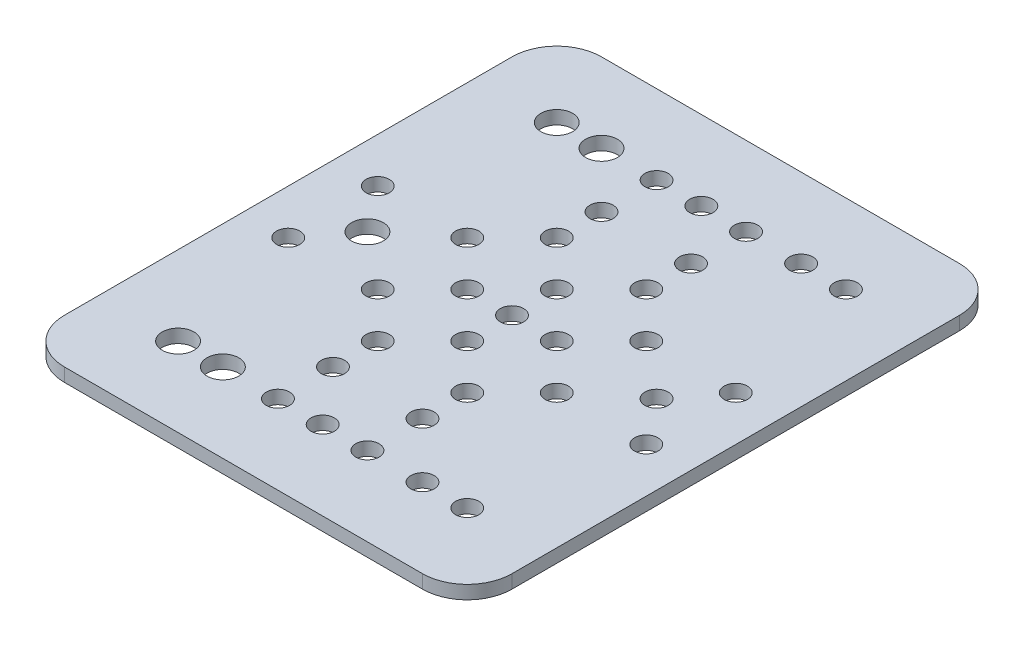
SolidWorks part; units mm, degrees
material "6061-T6 (SS)"
ref_plane "Front Plane" through (0, 0, 0) normal (0, 0, 1) x (1, 0, 0)
ref_plane "Top Plane" through (0, 0, 0) normal (0, 1, 0) x (1, 0, 0)
ref_plane "Right Plane" through (0, 0, 0) normal (1, 0, 0) x (0, 0, -1)
sketch "Sketch1" plane through (0, 0, 0) normal (0, 1, 0) x (1, 0, 0)
  line L0 (0, 0) -> (50, 0) construction
  line L1 (40, -60) -> (-40, -60)
  line L2 (50, -50) -> (50, 50)
  line L3 (40, 60) -> (-40, 60)
  line L4 (-50, -50) -> (-50, 50)
  line L5 (0, 60) -> (0, 0) construction
  arc A0 (-40, -60) -> (-50, -50) centre (-40, -50) cw
  arc A1 (40, -60) -> (50, -50) centre (40, -50) ccw
  arc A2 (50, 50) -> (40, 60) centre (40, 50) ccw
  arc A3 (-40, 60) -> (-50, 50) centre (-40, 50) ccw
  circle A4 centre (-22.3, 42.3) radius 3.55
  circle A5 centre (0, 10) radius 2.6
  circle A6 centre (0, 0) radius 2.6
  circle A7 centre (10, 0) radius 2.6
  circle A8 centre (-10, 0) radius 2.6
  circle A9 centre (-32.3, 42.3) radius 3.55
  circle A10 centre (-32.3, 0) radius 3.55
  circle A11 centre (-32.3, -42.3) radius 3.55
  circle A12 centre (-20, 10) radius 2.6
  circle A13 centre (-40, 10) radius 2.6
  circle A14 centre (-10, 20) radius 2.6
  circle A15 centre (-10, 30) radius 2.6
  circle A16 centre (-10, 42.3) radius 2.6
  circle A17 centre (0, 42.3) radius 2.6
  circle A18 centre (10, 42.3) radius 2.6
  circle A19 centre (10, 30) radius 2.6
  circle A20 centre (10, 20) radius 2.6
  circle A21 centre (20, 10) radius 2.6
  circle A22 centre (40, 10) radius 2.6
  circle A23 centre (22.3, 42.3) radius 2.6
  circle A24 centre (32.3, 42.3) radius 2.6
  circle A25 centre (32.3, 0) radius 2.6
  circle A26 centre (40, -10) radius 2.6
  circle A27 centre (32.3, -42.3) radius 2.6
  circle A28 centre (22.3, -42.3) radius 2.6
  circle A29 centre (20, -10) radius 2.6
  circle A30 centre (0, -10) radius 2.6
  circle A31 centre (10, -20) radius 2.6
  circle A32 centre (10, -30) radius 2.6
  circle A33 centre (10, -42.3) radius 2.6
  circle A34 centre (0, -42.3) radius 2.6
  circle A35 centre (-10, -42.3) radius 2.6
  circle A36 centre (-10, -30) radius 2.6
  circle A37 centre (-10, -20) radius 2.6
  circle A38 centre (-20, -10) radius 2.6
  circle A39 centre (-40, -10) radius 2.6
  circle A40 centre (-22.3, -42.3) radius 3.55
  point P0 (0, 0)
  dimension "D2" = 10
  dimension "D3" = 5.2
  dimension "D5" = 7.1
  dimension "D7" = 10
  dimension "D10" = 10
  dimension "D1" = 120
  dimension "D4" = 10
  dimension "D6" = 84.6
  dimension "D8" = 17.7
  dimension "D9" = 100
  dimension "D11" = 20
  dimension "D12" = 20
  dimension "D13" = 20
  dimension "D14" = 10
  dimension "D15" = 10
  dimension "D16" = 64.6
  dimension "D17" = 10
extrude "Boss-Extrude1" add sketch "Sketch1" along normal blind 3
